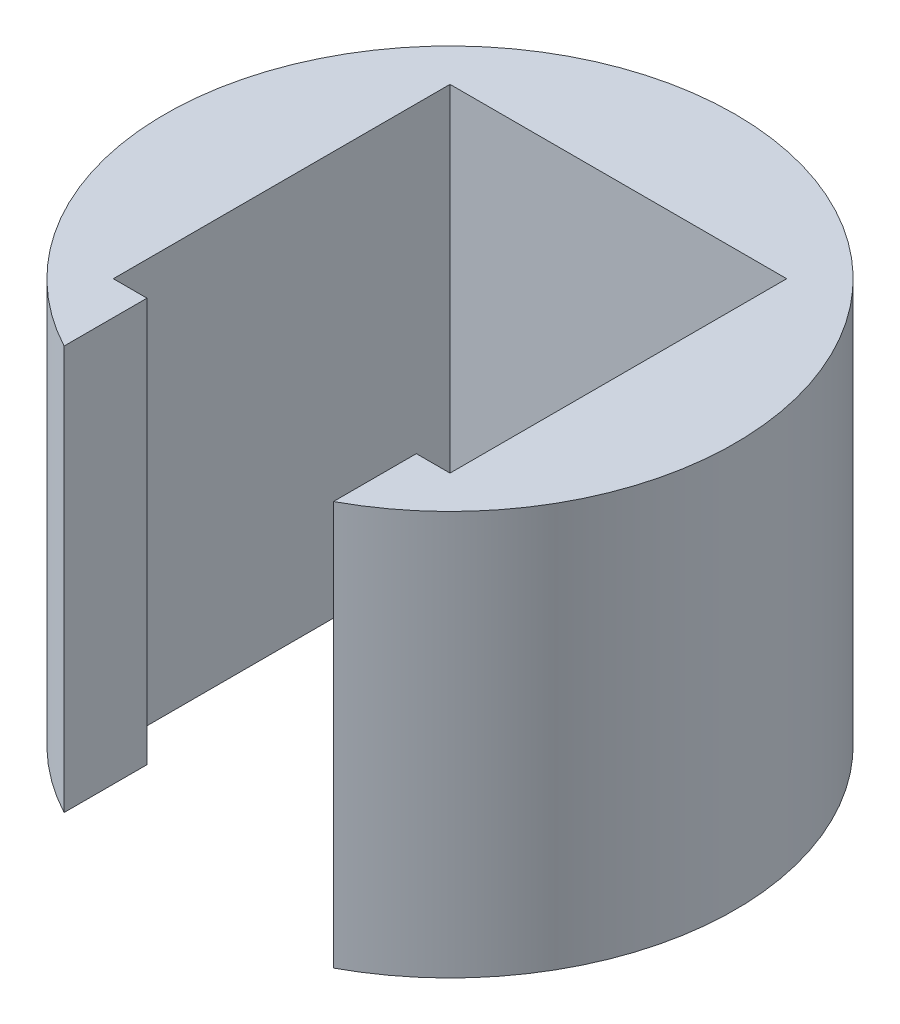
SolidWorks part; units mm, degrees
ref_plane "Front Plane" through (0, 0, 0) normal (0, 0, 1) x (1, 0, 0)
ref_plane "Top Plane" through (0, 0, 0) normal (0, 1, 0) x (1, 0, 0)
ref_plane "Right Plane" through (0, 0, 0) normal (1, 0, 0) x (0, 0, -1)
sketch "Sketch1" plane through (0, 0, 0) normal (0, 1, 0) x (1, 0, 0)
  line L0 (5.9996, -7.5) -> (7.5, -7.5)
  line L1 (-7.5, 7.5) -> (7.5, 7.5)
  line L2 (-7.5, 7.5) -> (-7.5, -7.5)
  line L3 (-7.5, -7.5) -> (-5.9996, -7.5)
  line L4 (7.5, 7.5) -> (7.5, -7.5)
  line L5 (-7.5, 7.5) -> (7.5, -7.5) construction
  line L6 (-7.5, -7.5) -> (7.5, 7.5) construction
  line L7 (-5.9996, -7.5) -> (-5.9996, -11.1935)
  line L9 (5.9996, -11.1935) -> (5.9996, -7.5)
  arc A0 (5.9996, -11.1935) -> (-5.9996, -11.1935) centre (0, 0) ccw
extrude "Boss-Extrude2" add sketch "Sketch1" along normal blind 18
